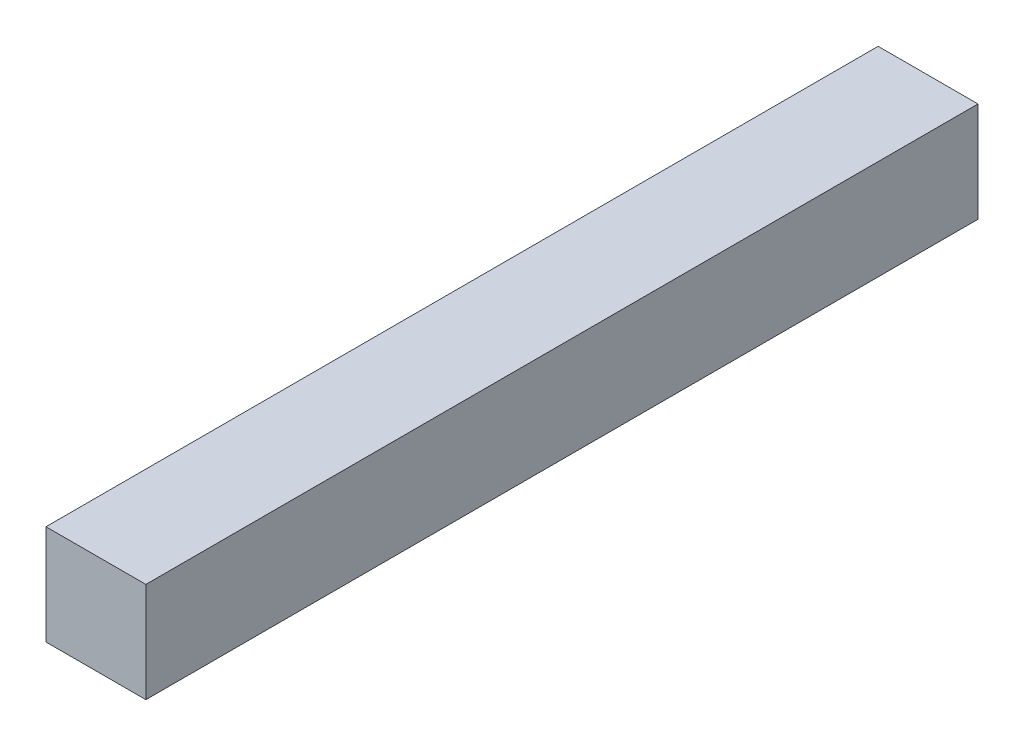
SolidWorks part; units mm, degrees
ref_plane "Front Plane" through (0, 0, 0) normal (0, 0, 1) x (1, 0, 0)
ref_plane "Top Plane" through (0, 0, 0) normal (0, 1, 0) x (1, 0, 0)
ref_plane "Right Plane" through (0, 0, 0) normal (1, 0, 0) x (0, 0, -1)
sketch "Sketch1" plane through (0, 0, 0) normal (0, 0, 1) x (1, 0, 0)
  line L1 (-3, 3) -> (3, 3)
  line L2 (-3, 3) -> (-3, -3)
  line L3 (-3, -3) -> (3, -3)
  line L4 (3, 3) -> (3, -3)
  line L5 (-3, 3) -> (3, -3) construction
  line L6 (-3, -3) -> (3, 3) construction
  point P1 (0, 0)
  dimension "D1" = 6
  dimension "D2" = 6
extrude "Boss-Extrude1" add sketch "Sketch1" along normal blind 50
